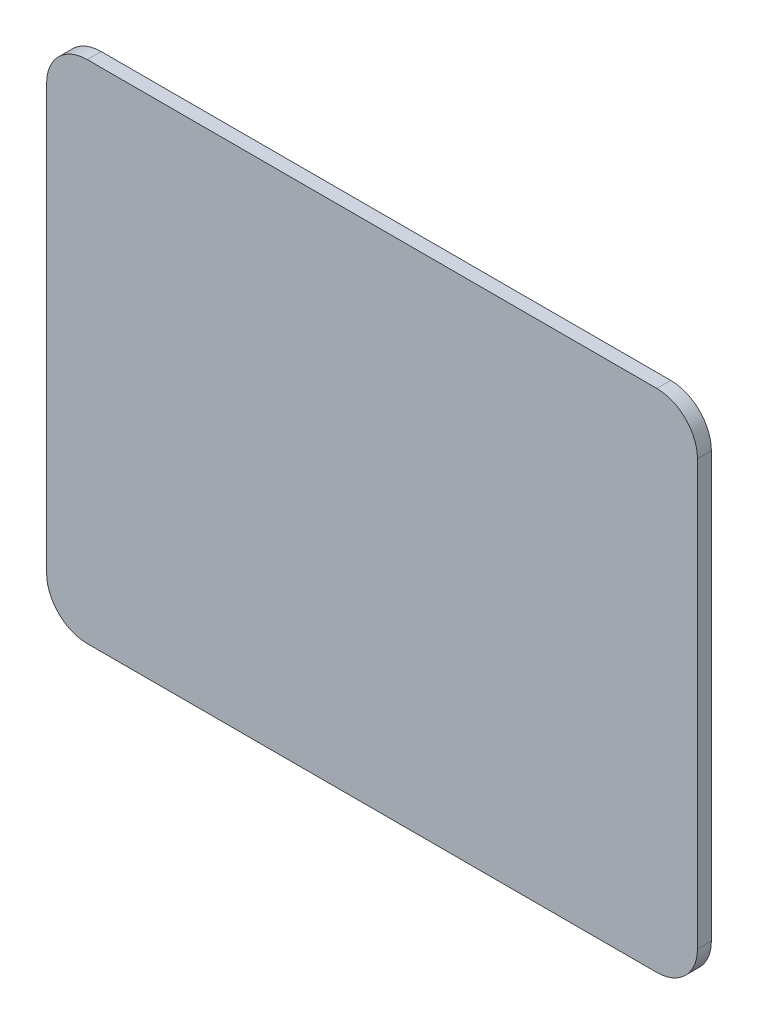
SolidWorks part; units mm, degrees
ref_plane "Front Plane" through (0, 0, 0) normal (0, 0, 1) x (1, 0, 0)
ref_plane "Top Plane" through (0, 0, 0) normal (0, 1, 0) x (1, 0, 0)
ref_plane "Right Plane" through (0, 0, 0) normal (1, 0, 0) x (0, 0, -1)
sketch "Sketch1" plane through (0, 0, 0) normal (0, 0, 1) x (1, 0, 0)
  line L1 (-92.8635, 25.26) -> (19.3365, 25.26)
  line L2 (-92.8635, 25.26) -> (-92.8635, -61.94)
  line L3 (-92.8635, -61.94) -> (19.3365, -61.94)
  line L4 (19.3365, 25.26) -> (19.3365, -61.94)
  dimension "D1" = 87.2
  dimension "D2" = 112.2
extrude "Boss-Extrude1" add sketch "Sketch1" along normal blind 2.4
fillet "Fillet2" radius 7 4 edges at (19.3365, -61.94, 1.2) (-92.8635, -61.94, 1.2) (-92.8635, 25.26, 1.2) (19.3365, 25.26, 1.2)
